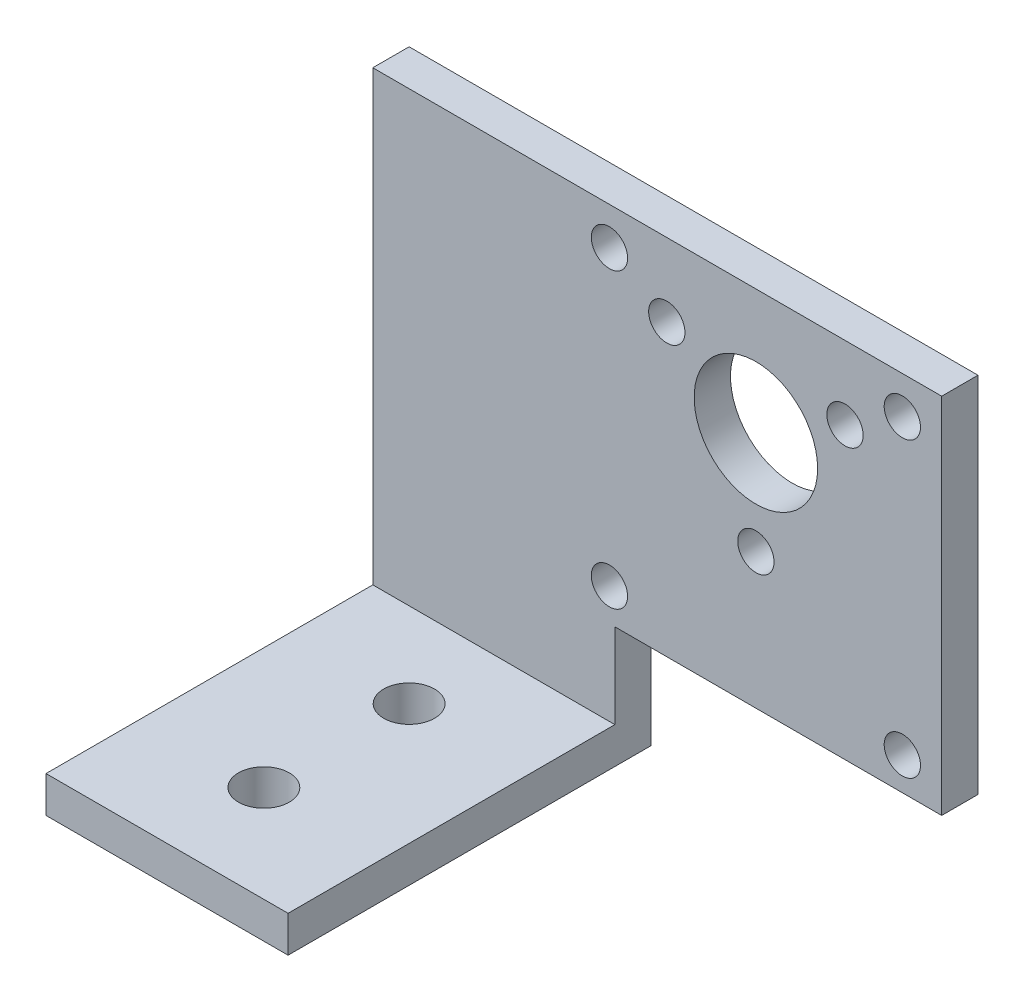
SolidWorks part; units mm, degrees
ref_plane "Plan de face" through (0, 0, 0) normal (0, 0, 1) x (1, 0, 0)
ref_plane "Plan de dessus" through (0, 0, 0) normal (0, 1, 0) x (1, 0, 0)
ref_plane "Plan de droite" through (0, 0, 0) normal (1, 0, 0) x (0, 0, -1)
sketch "Esquisse1" plane through (0, 0, 0) normal (0, 0, 1) x (1, 0, 0)
  line L0 (-11.65, -19.7) -> (15.35, -19.7)
  line L1 (15.35, -19.7) -> (15.35, 10.3)
  line L2 (15.35, 10.3) -> (-31.65, 10.3)
  line L3 (-31.65, 10.3) -> (-31.65, -29.7)
  line L4 (-31.65, -29.7) -> (-11.65, -29.7)
  line L5 (-11.65, -29.7) -> (-11.65, -19.7)
  line L6 (0, 0) -> (0, -8.5) construction
  line L7 (-12.1, 7.2) -> (12.1, 7.2) construction
  line L8 (-12.1, 7.2) -> (-12.1, -17) construction
  line L9 (-12.1, -17) -> (12.1, -17) construction
  line L10 (12.1, 7.2) -> (12.1, -17) construction
  line L11 (0, 0) -> (7.3612, 4.25) construction
  line L12 (0, 0) -> (-7.3612, 4.25) construction
  circle A0 centre (0, 0) radius 5.1
  circle A1 centre (-12.1, 7.2) radius 1.5
  circle A2 centre (-12.1, -17) radius 1.5
  circle A3 centre (12.1, -17) radius 1.5
  circle A4 centre (12.1, 7.2) radius 1.5
  circle A5 centre (0, 0) radius 8.5 construction
  circle A6 centre (0, -8.5) radius 1.5
  circle A7 centre (-7.3612, 4.25) radius 1.5
  circle A8 centre (7.3612, 4.25) radius 1.5
  dimension "D2" = 3
  dimension "D9" = 7.2
  dimension "D10" = 10.2
  dimension "D13" = 3
  dimension "D14" = 17
  dimension "D1" = 47
  dimension "D3" = 24.2
  dimension "D4" = 24.2
  dimension "D5" = 3.1
  dimension "D6" = 40
  dimension "D7" = 20
  dimension "D8" = 12.1
  dimension "D11" = 19.55
  dimension "D12" = 10
  dimension "D15" = 120
  dimension "D16" = 120
extrude "Extrusion1" add sketch "Esquisse1" along normal blind 3
sketch "Esquisse2" plane through (0, 0, 3) normal (0, 0, 1) x (1, 0, 0)
  line L0 (-31.65, 10.3) -> (-31.65, -29.7) construction
  line L1 (-11.65, -29.7) -> (-31.65, -29.7)
  line L2 (-11.65, -29.7) -> (-11.65, -26.7)
  line L3 (-11.65, -26.7) -> (-31.65, -26.7)
  line L4 (-31.65, -29.7) -> (-31.65, -26.7)
  dimension "D1" = 3
extrude "Extrusion2" add sketch "Esquisse2" along normal blind 27
sketch "Esquisse4" plane through (0, -26.7, 0) normal (0, 1, 0) x (-1, 0, 0)
  line L0 (21.65, 10) -> (21.65, 22) construction
  line L1 (11.65, 30) -> (11.65, 3) construction
  line L2 (21.65, 30) -> (21.65, 22) construction
  line L3 (11.65, 30) -> (31.65, 30) construction
  circle A0 centre (21.65, 10) radius 2.1
  circle A1 centre (21.65, 22) radius 2.1
  dimension "D1" = 4.2
  dimension "D2" = 8
  dimension "D3" = 12
extrude "Enlèv. mat.-Extru.1" cut sketch "Esquisse4" against normal through all
